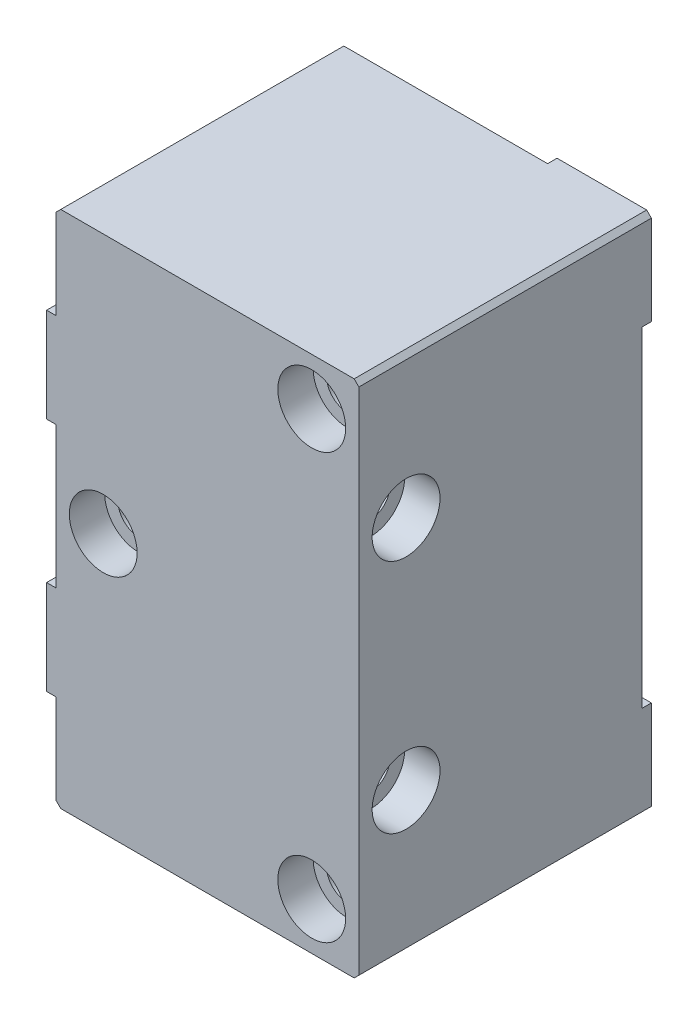
SolidWorks part; units mm, degrees
material "AISI 304"
ref_plane "Front Plane" through (0, 0, 0) normal (0, 0, 1) x (1, 0, 0)
ref_plane "Top Plane" through (0, 0, 0) normal (0, 1, 0) x (1, 0, 0)
ref_plane "Right Plane" through (0, 0, 0) normal (1, 0, 0) x (0, 0, -1)
sketch "Sketch1" plane through (0, 0, 0) normal (0, 0, 1) x (1, 0, 0)
  line L1 (-36.6688, 34.2774) -> (44.8652, 34.2774)
  line L2 (-36.6688, 34.2774) -> (-36.6688, -105.4226)
  line L3 (-36.6688, -105.4226) -> (44.8652, -105.4226)
  line L4 (44.8652, 34.2774) -> (44.8652, -105.4226)
  dimension "D1" = 81.534
  dimension "D2" = 139.7
extrude "Extrude1" add sketch "Sketch1" along normal blind 76.2
sketch "Sketch8" plane through (0, 0, 0) normal (0, 0, -1) x (-1, 0, 0)
  line L0 (36.6688, 34.2774) -> (36.6688, -105.4226) construction
  line L1 (-44.8652, -105.4226) -> (-19.4652, -105.4226)
  line L2 (-44.8652, -105.4226) -> (-44.8652, -80.0226)
  line L3 (-44.8652, -80.0226) -> (-19.4652, -80.0226)
  line L4 (-19.4652, -105.4226) -> (-19.4652, -80.0226)
  line L5 (-44.8652, 34.2774) -> (-19.4652, 34.2774)
  line L6 (-44.8652, 34.2774) -> (-44.8652, 8.8774)
  line L7 (-44.8652, 8.8774) -> (-19.4652, 8.8774)
  line L8 (-19.4652, 34.2774) -> (-19.4652, 8.8774)
  line L9 (36.6688, -22.8726) -> (11.2688, -22.8726)
  line L10 (36.6688, -22.8726) -> (36.6688, -48.2726)
  line L11 (36.6688, -48.2726) -> (11.2688, -48.2726)
  line L12 (11.2688, -22.8726) -> (11.2688, -48.2726)
  line L13 (-44.8652, 34.2774) -> (36.6688, 34.2774) construction
  dimension "D1" = 25.4
  dimension "D2" = 25.4
  dimension "D3" = 57.15
extrude "Extrude2" add sketch "Sketch8" along normal blind 2.54
hole_wizard "CBORE for 3/8 Socket Head Cap Screw1" positions "Sketch3" profile "Sketch2" counterbore size "3/8" standard "Ansi Inch" end condition through all
sketch "Sketch3" plane through (0, 0, 76.2) normal (0, 0, 1) x (1, 0, 0)
  line L10 (19.4652, 34.2774) -> (44.8652, 34.2774) construction
  line L11 (44.8652, 34.2774) -> (44.8652, 8.8774) construction
  line L12 (44.8652, -80.0226) -> (44.8652, -105.4226) construction
  line L13 (44.8652, -105.4226) -> (19.4652, -105.4226) construction
  line L14 (19.4652, 34.2774) -> (-36.6688, 34.2774) construction
  line L15 (-36.6688, -48.2726) -> (-36.6688, -22.8726) construction
  point P0 (-23.9688, -35.5726)
  point P1 (32.1652, 21.5774)
  point P5 (32.1652, -92.7226)
  point P39 (32.1652, 34.2774)
  dimension "D1" = 12.7
  dimension "D2" = 12.7
  dimension "D3" = 12.7
  dimension "D4" = 12.7
  dimension "D5" = 69.85
  dimension "D6" = 12.7
sketch "Sketch2" plane through (-23.9688, -35.5726, 76.2) normal (1, 0, 0) x (0, -1, 0)
  line L0 (0, 0) -> (0, 78.74)
  line L1 (0, 78.74) -> (5.5499, 78.74)
  line L3 (5.5499, 78.74) -> (5.5499, 9.525)
  line L4 (5.5499, 9.525) -> (9.1313, 9.525)
  line L5 (9.1313, 9.525) -> (9.1313, 0)
  line L7 (9.1313, 0) -> (0, 0)
  line L11 (0, -6.35) -> (0, 107.95) construction
  dimension "Thru Hole Dia." = 11.0998
  dimension "Thru Hole Depth" = 78.74
  dimension "C'Bore Dia." = 18.2626
  dimension "C'Bore Depth" = 9.525
sketch "Sketch9" plane through (-36.6688, 0, 0) normal (-1, 0, 0) x (0, 0, 1)
  line L0 (76.2, 34.2774) -> (76.2, -105.4226) construction
  line L1 (76.2, 8.8774) -> (50.8, 8.8774)
  line L2 (76.2, 8.8774) -> (76.2, -16.5226)
  line L3 (76.2, -16.5226) -> (50.8, -16.5226)
  line L4 (50.8, 8.8774) -> (50.8, -16.5226)
  line L5 (76.2, 34.2774) -> (0, 34.2774) construction
  line L6 (76.2, -80.0226) -> (50.8, -80.0226)
  line L7 (76.2, -80.0226) -> (76.2, -54.6226)
  line L8 (76.2, -54.6226) -> (50.8, -54.6226)
  line L9 (50.8, -80.0226) -> (50.8, -54.6226)
  line L10 (76.2, -105.4226) -> (0, -105.4226) construction
  dimension "D1" = 25.4
  dimension "D2" = 25.4
  dimension "D3" = 25.4
  dimension "D4" = 25.4
extrude "Extrude3" add sketch "Sketch9" along normal blind 2.54
hole_wizard "CBORE for 3/8 Socket Head Cap Screw3" positions "Sketch7" profile "Sketch6" counterbore size "3/8" standard "Ansi Inch" end condition through all
sketch "Sketch7" plane through (44.8652, 0, 0) normal (1, 0, 0) x (0, 0, -1)
  line L2 (-76.2, -105.4226) -> (-76.2, 34.2774) construction
  line L7 (-63.5, -3.8226) -> (-63.5, -67.3226) construction
  line L12 (-76.2, 34.2774) -> (2.54, 34.2774) construction
  line L13 (-76.2, -105.4226) -> (2.54, -105.4226) construction
  point P1 (-63.5, -3.8226)
  point P3 (-63.5, -67.3226)
  dimension "D1" = 12.7
  dimension "D2" = 38.1
  dimension "D3" = 38.1
sketch "Sketch6" plane through (44.8652, -3.8226, 63.5) normal (0, 1, 0) x (0, 0, -1)
  line L0 (0, 0) -> (0, 84.074)
  line L1 (0, 84.074) -> (5.1562, 84.074)
  line L3 (5.1562, 84.074) -> (5.1562, 9.525)
  line L4 (5.1562, 9.525) -> (9.1313, 9.525)
  line L5 (9.1313, 9.525) -> (9.1313, 0)
  line L7 (9.1313, 0) -> (0, 0)
  line L11 (0, -6.35) -> (0, 107.95) construction
  dimension "Thru Hole Dia." = 10.3124
  dimension "Thru Hole Depth" = 84.074
  dimension "C'Bore Dia." = 18.2626
  dimension "C'Bore Depth" = 9.525
chamfer "Chamfer1" distance 1.27 angle 45 4 edges at (44.8652, 34.2774, 36.83) (-36.6688, 34.2774, 38.1) (44.8652, -105.4226, 36.83) (-36.6688, -105.4226, 38.1)
